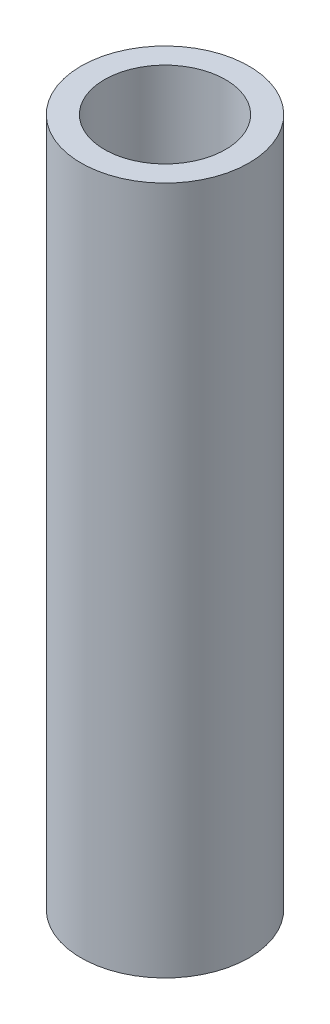
SolidWorks part; units mm, degrees
ref_plane "Front Plane" through (0, 0, 0) normal (0, 0, 1) x (1, 0, 0)
ref_plane "Top Plane" through (0, 0, 0) normal (0, 1, 0) x (1, 0, 0)
ref_plane "Right Plane" through (0, 0, 0) normal (1, 0, 0) x (0, 0, -1)
sketch "Sketch1" plane through (0, 0, 0) normal (0, 0, 1) x (1, 0, 0)
  line L0 (-15.25, 62.5) -> (-15.25, -62.5)
  line L2 (0, 83.1835) -> (0, -85.2818) construction
  line L3 (-11, 62.5) -> (-11, -62.5)
  line L4 (-15.25, -62.5) -> (-11, -62.5)
  line L5 (-15.25, 62.5) -> (-11, 62.5)
  point P5 (-11, 0)
  dimension "D1" = 125
  dimension "D2" = 30.5
  dimension "D3" = 4.25
revolve "Revolve1" add sketch "Sketch1" angle 360 about L2
